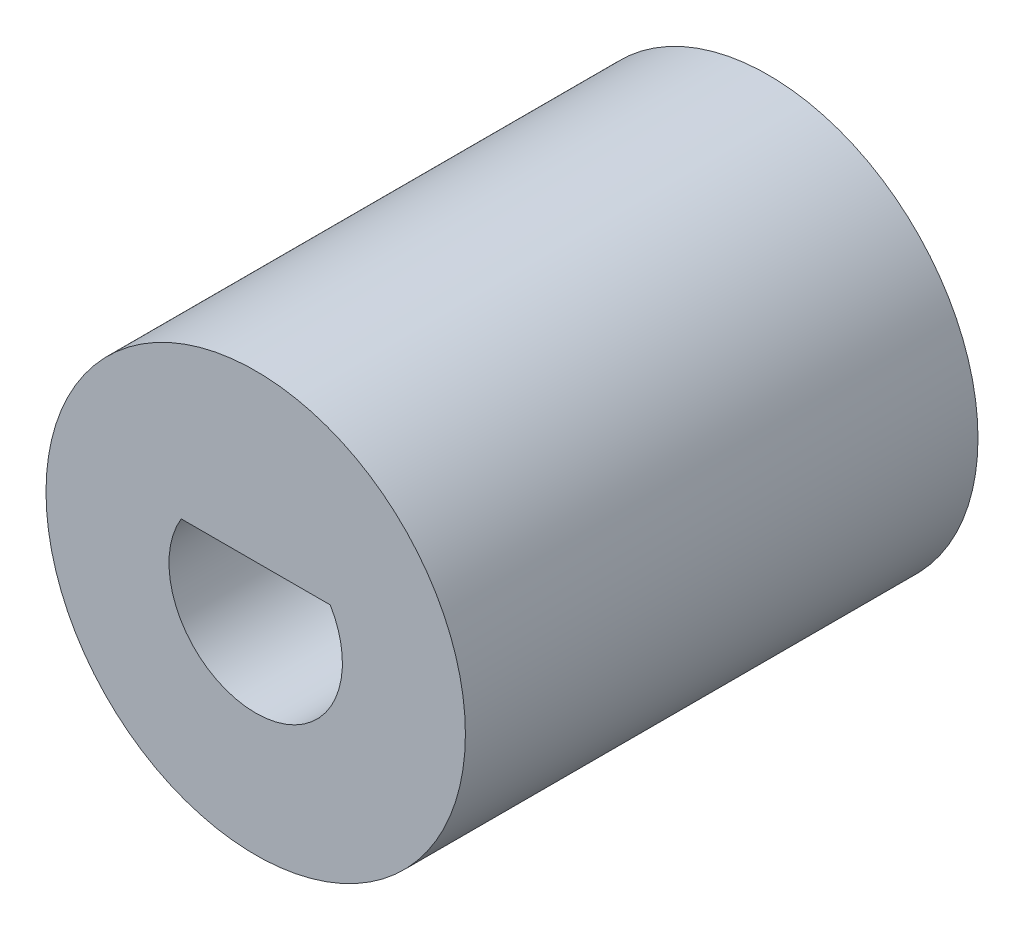
SolidWorks part; units mm, degrees
ref_plane "Front Plane" through (0, 0, 0) normal (0, 0, 1) x (1, 0, 0)
ref_plane "Top Plane" through (0, 0, 0) normal (0, 1, 0) x (1, 0, 0)
ref_plane "Right Plane" through (0, 0, 0) normal (1, 0, 0) x (0, 0, -1)
sketch "Sketch1" plane through (0, 0, 0) normal (0, 0, 1) x (1, 0, 0)
  circle A0 centre (0, 9.1456) radius 4.5
extrude "Boss-Extrude1" add sketch "Sketch1" along normal blind 11
sketch "Sketch6" plane through (0, 0, 0) normal (0, 0, -1) x (-1, 0, 0)
  line L1 (3.2909, 9.1456) -> (1.6454, 11.9956)
  line L2 (1.6454, 11.9956) -> (-1.6454, 11.9956)
  line L3 (-1.6454, 11.9956) -> (-3.2909, 9.1456)
  line L4 (-3.2909, 9.1456) -> (-1.6454, 6.2956)
  line L5 (-1.6454, 6.2956) -> (1.6454, 6.2956)
  line L6 (1.6454, 6.2956) -> (3.2909, 9.1456)
  circle A0 centre (0, 9.1456) radius 2.85 construction
  dimension "D1" = 5.7
extrude "Cut-Extrude3" cut sketch "Sketch6" against normal blind 2
sketch "Sketch7" plane through (0, 0, 0) normal (0, 0, -1) x (-1, 0, 0)
  line L0 (0, 7.3456) -> (0, 10.0956) construction
  line L1 (1.6, 10.0956) -> (-1.6, 10.0956)
  arc A1 (1.6, 10.0956) -> (-1.6, 10.0956) centre (0, 9.1456) cw
extrude "Cut-Extrude4" cut sketch "Sketch7" against normal through all
